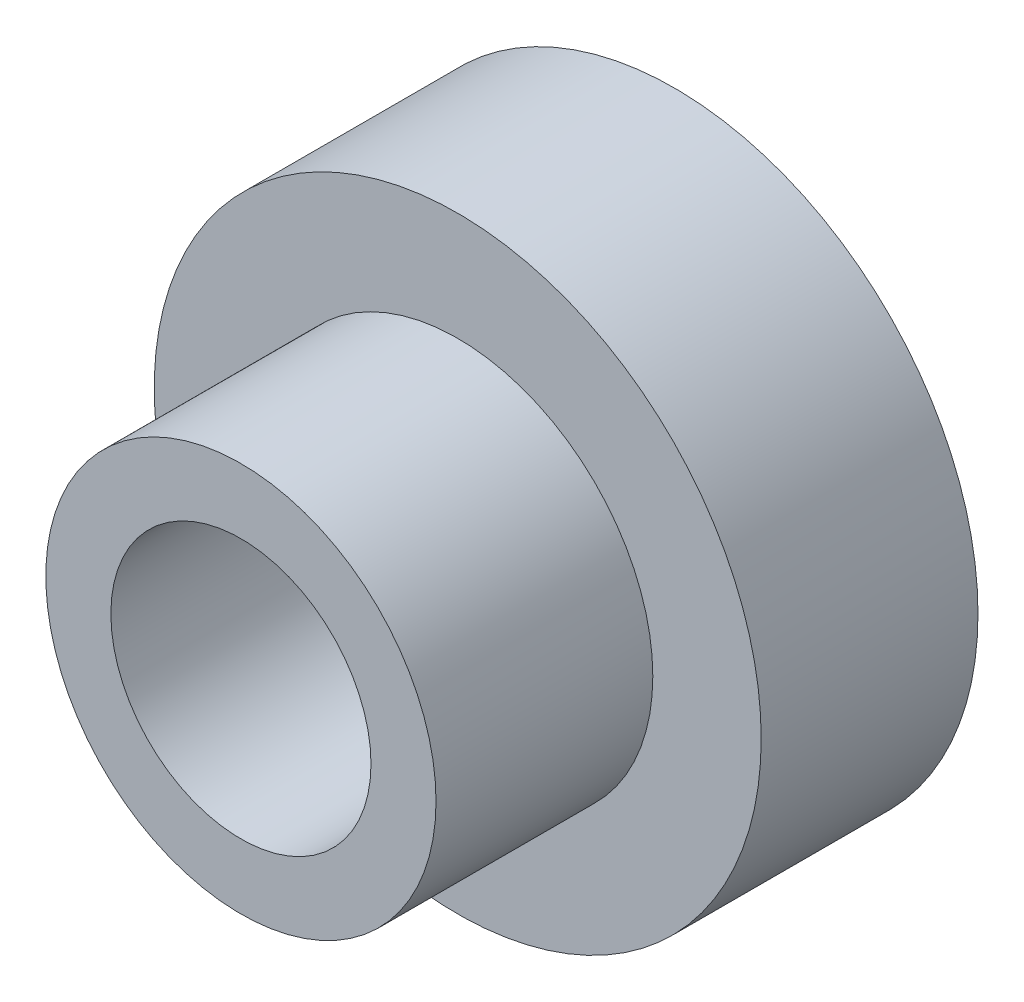
SolidWorks part; units mm, degrees
ref_plane "前视基准面" through (0, 0, 0) normal (0, 0, 1) x (1, 0, 0)
ref_plane "上视基准面" through (0, 0, 0) normal (0, 1, 0) x (1, 0, 0)
ref_plane "右视基准面" through (0, 0, 0) normal (1, 0, 0) x (0, 0, -1)
sketch "草图1" plane through (0, 0, 0) normal (0, 0, 1) x (1, 0, 0)
  circle A0 centre (0, 0) radius 14
  dimension "D1" = 28
extrude "凸台-拉伸1" add sketch "草图1" along normal blind 10
sketch "草图2" plane through (0, 0, 10) normal (0, 0, 1) x (1, 0, 0)
  circle A0 centre (0, 0) radius 9
  dimension "D1" = 18
extrude "凸台-拉伸2" add sketch "草图2" along normal blind 10
sketch "草图3" plane through (0, 0, 20) normal (0, 0, 1) x (1, 0, 0)
  circle A0 centre (0, 0) radius 6
  dimension "D1" = 12
extrude "切除-拉伸1" cut sketch "草图3" against normal through all
